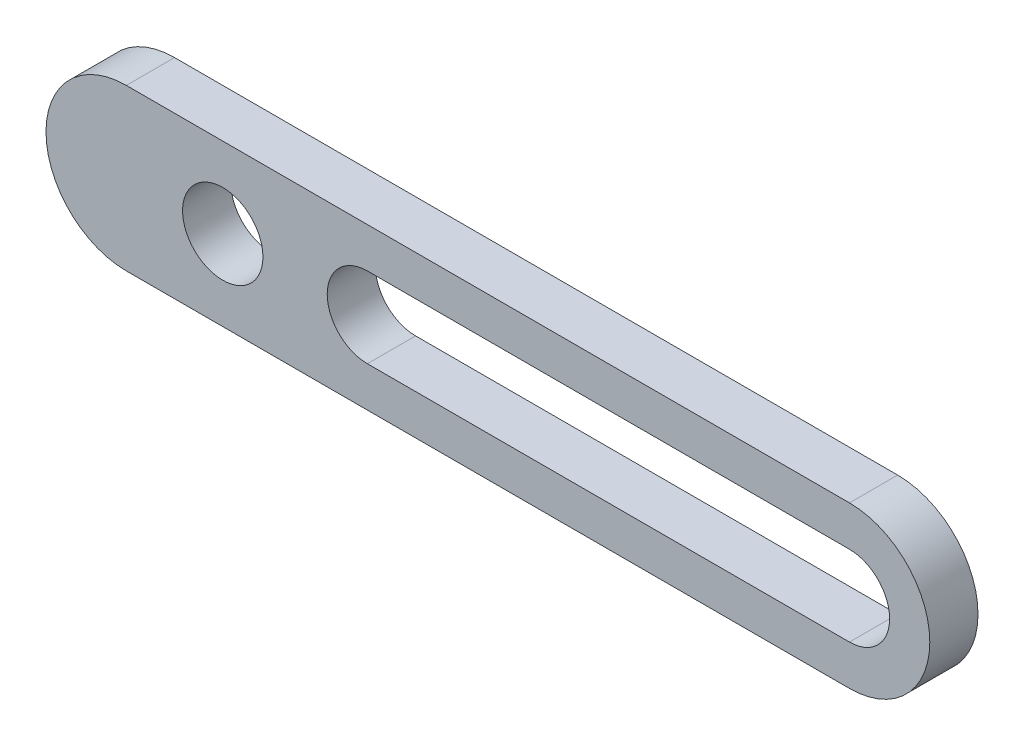
SolidWorks part; units mm, degrees
ref_plane "Front Plane" through (0, 0, 0) normal (0, 0, 1) x (1, 0, 0)
ref_plane "Top Plane" through (0, 0, 0) normal (0, 1, 0) x (1, 0, 0)
ref_plane "Right Plane" through (0, 0, 0) normal (1, 0, 0) x (0, 0, -1)
sketch "Sketch2" plane through (0, 0, 0) normal (0, 0, 1) x (1, 0, 0)
  line L0 (8.1525, 0.8557) -> (54.3236, 0.8557) construction
  line L1 (17.1525, 3.3557) -> (47.1525, 3.3557)
  line L2 (17.1525, -1.6443) -> (47.1525, -1.6443)
  line L3 (2.1525, 5.8557) -> (47.1525, 5.8557)
  line L4 (2.1525, -4.1443) -> (47.1525, -4.1443)
  line L5 (2.1525, 3.3557) -> (47.1525, 3.3557) construction
  line L6 (2.1525, -1.6443) -> (47.1525, -1.6443) construction
  line L7 (14.6525, 0.8557) -> (47.1525, 0.8557) construction
  arc A1 (47.1525, -1.6443) -> (47.1525, 3.3557) centre (47.1525, 0.8557) ccw
  arc A2 (47.1525, -4.1443) -> (47.1525, 5.8557) centre (47.1525, 0.8557) ccw
  arc A3 (2.1525, 5.8557) -> (2.1525, -4.1443) centre (2.1525, 0.8557) ccw
  circle A4 centre (8.1525, 0.8557) radius 2.5
  arc A6 (17.1525, 3.3557) -> (17.1525, -1.6443) centre (17.1525, 0.8557) ccw
  arc A7 (2.1525, 3.3557) -> (2.1525, -1.6443) centre (2.1525, 0.8557) ccw construction
  point P3 (25, 0)
  point P16 (5.7623, 0.8557)
  point P17 (6.7776, 0.8557)
  dimension "D2" = 30
  dimension "D3" = 45
  dimension "D5" = 5
  dimension "D6" = 2.5
  dimension "D7" = 2.5
  dimension "D1" = 2.5
  dimension "D4" = 6
extrude "Boss-Extrude1" add sketch "Sketch2" along normal blind 3
